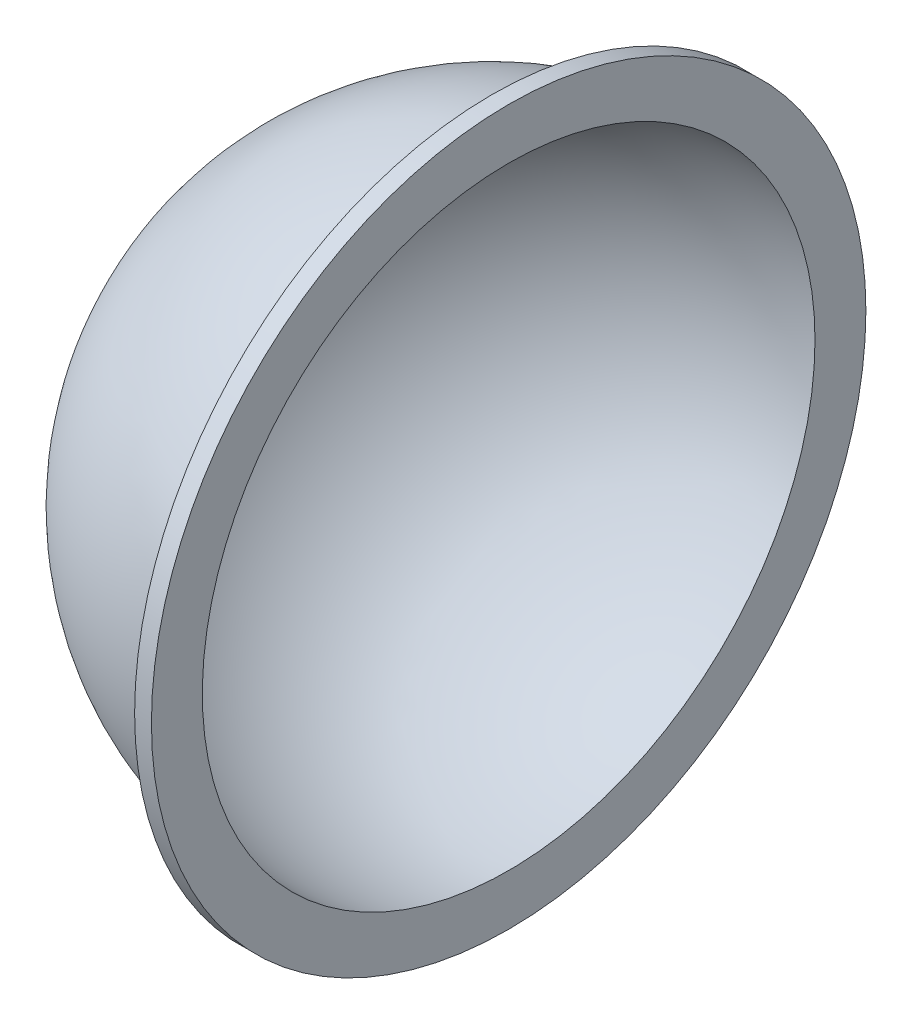
SolidWorks part; units mm, degrees
ref_plane "Front Plane" through (0, 0, 0) normal (0, 0, 1) x (1, 0, 0)
ref_plane "Top Plane" through (0, 0, 0) normal (0, 1, 0) x (1, 0, 0)
ref_plane "Right Plane" through (0, 0, 0) normal (1, 0, 0) x (0, 0, -1)
sketch "Sketch1" plane through (0, 0, 0) normal (0, 0, 1) x (1, 0, 0)
  line L0 (0, 36.5) -> (0, 57.3704)
  line L1 (0, 0) -> (-57.2513, 0)
  line L2 (0, 0) -> (2, 0)
  line L3 (2, 36.4452) -> (2, 57.3704)
  line L4 (2, -2) -> (-57.2513, -2) construction
  line L5 (2, -2) -> (2, 57.3704) construction
  line L6 (0, 42.5) -> (2, 42.5)
  line L7 (0, 0) -> (0, 57.3704) construction
  arc A0 (2, 37.4466) -> (-37.5, 0) centre (0, 0) ccw
  arc A1 (2, 36.4452) -> (-36.5, 0) centre (0, 0) ccw
  dimension "D1" = 2
  dimension "D2" = 42.5
  dimension "D3" = 75
  dimension "D4" = 73
revolve "Revolve1" add sketch "Sketch1" angle 360 about L1
